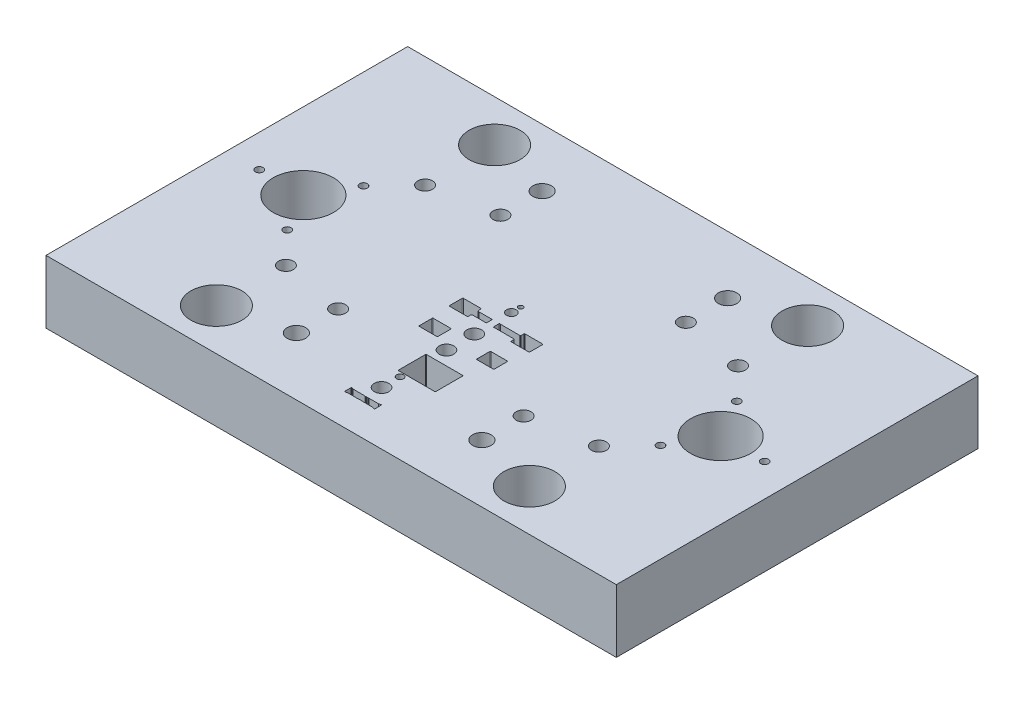
SolidWorks part; units mm, degrees
ref_plane "Front" through (0, 0, 0) normal (0, 0, 1) x (1, 0, 0)
ref_plane "Top" through (0, 0, 0) normal (0, 1, 0) x (1, 0, 0)
ref_plane "Right" through (0, 0, 0) normal (1, 0, 0) x (0, 0, -1)
sketch "Sketch1" plane through (0, 0, 0) normal (0, 0, 1) x (1, 0, 0)
  line L1 (-123, 0) -> (123, 0)
  line L2 (-123, 0) -> (-123, 27.2)
  line L3 (-123, 27.2) -> (123, 27.2)
  line L4 (123, 0) -> (123, 27.2)
  dimension "D1" = 246
  dimension "D2" = 27.2
extrude "Extrude1" add sketch "Sketch1" along normal mid plane 156
hole_wizard "Hole4" positions "Sketch9" profile "Sketch8" legacy
sketch "Sketch9" plane through (0, 0, 0) normal (0, -1, 0) x (1, 0, 0)
  line L0 (0, 0) -> (0, 38.3553) construction
  point P0 (90, 0)
  dimension "D1" = 180
sketch "Sketch8" plane through (90, 0, 0) normal (1, 0, 0) x (0, 0, -1)
  line L0 (0, 0) -> (0, 30)
  line L1 (0, 30) -> (13, 30)
  line L2 (13, 30) -> (13, 0)
  line L3 (13, 0) -> (0, 0)
  line L4 (0, 110) -> (0, -10) construction
  dimension "Diameter" = 26
  dimension "Depth" = 30
pattern_linear "LPattern4" count 2 spacing 180 along (-1, 0, 0) of "Hole4"
sketch "Sketch10" plane through (0, 0, 0) normal (0, 0, 1) x (1, 0, 0)
  line L1 (52.5, 27.2) -> (-52.5, 27.2)
  line L2 (52.5, 27.2) -> (52.5, 17.2)
  line L3 (52.5, 17.2) -> (-52.5, 17.2)
  line L4 (-52.5, 27.2) -> (-52.5, 17.2)
  line L5 (0, 17.2) -> (0, 0) construction
  line L6 (123, 27.2) -> (-123, 27.2) construction
  dimension "D1" = 10
  dimension "D2" = 105
extrude "Cut-Extrude1" [suppressed] cut sketch "Sketch10" against normal mid plane 206
hole_wizard "Hole5" positions "Sketch13" profile "Sketch12" legacy
sketch "Sketch13" plane through (0, 0, 0) normal (0, -1, 0) x (1, 0, 0)
  point P0 (-67.5, -30)
  dimension "D1" = 30
  dimension "D2" = 67.5
sketch "Sketch12" plane through (-67.5, 0, -30) normal (1, 0, 0) x (0, 0, -1)
  line L0 (0, 0) -> (0, 100)
  line L1 (0, 100) -> (3.2, 100)
  line L2 (3.2, 100) -> (3.2, 12)
  line L3 (3.2, 12) -> (12.5, 12)
  line L4 (12.5, 12) -> (12.5, 0)
  line L5 (12.5, 0) -> (0, 0)
  line L6 (0, 110) -> (0, -10) construction
  dimension "Diameter" = 6.4
  dimension "Depth" = 100
  dimension "C-Bore Diameter" = 25
  dimension "C-Bore Depth" = 12
cosmetic thread "Cosmetic Thread1" parameters "D2"=8
sketch "Sketch17" plane through (0, 0, 0) normal (0, -1, 0) x (1, 0, 0)
  line L0 (-20, 0) -> (20, 0) construction
  line L2 (-20, 70) -> (-20, -70)
  line L3 (-15, -75) -> (15, -75)
  line L4 (20, 70) -> (20, -70)
  line L6 (-15, 75) -> (15, 75)
  arc A0 (20, -70) -> (15, -75) centre (15, -70) cw
  arc A1 (-15, -75) -> (-20, -70) centre (-15, -70) cw
  arc A2 (15, 75) -> (20, 70) centre (15, 70) cw
  arc A5 (-15, 75) -> (-20, 70) centre (-15, 70) ccw
  point P8 (20, -75)
  point P13 (-50, 90)
  point P16 (50, 90)
  dimension "D4" = 5
  dimension "D1" = 75
  dimension "D2" = 75
  dimension "D3" = 40
extrude "Cut-Extrude4" cut sketch "Sketch17" against normal blind 1
pattern_linear "LPattern5" count 2 spacing 60 along (0, 0, 1) count 2 spacing 135 along (1, 0, 0) of "Hole5"
hole_wizard "CBORE for M6 Hex Socket Head Cap Screw1" positions "Sketch19" profile "Sketch18" counterbore size "M6" standard "ISO" end condition through all
sketch "Sketch19" plane through (0, 0, 0) normal (0, -1, 0) x (1, 0, 0)
  point P1 (40, 35)
  point P4 (40, -35)
  point P13 (-40, -35)
  point P16 (-40, 35)
sketch "Sketch18" plane through (40, 0, 35) normal (1, 0, 0) x (0, 0, -1)
  line L0 (0, 0) -> (0, 27.2)
  line L1 (0, 27.2) -> (3.2, 27.2)
  line L3 (3.2, 27.2) -> (3.2, 8)
  line L4 (3.2, 8) -> (5.5, 8)
  line L5 (5.5, 8) -> (5.5, 0)
  line L7 (5.5, 0) -> (0, 0)
  line L11 (0, -6.35) -> (0, 107.95) construction
  dimension "Thru Hole Dia." = 6.4
  dimension "Thru Hole Depth" = 27.2
  dimension "C'Bore Dia." = 11
  dimension "C'Bore Depth" = 8
hole_wizard "Hole6" positions "Sketch21" profile "Sketch20" legacy end condition through all
sketch "Sketch21" plane through (0, 0, 0) normal (0, -1, 0) x (1, 0, 0)
  point P1 (40, 53)
  point P8 (-40, 53)
  point P11 (-40, -53)
  point P14 (40, -53)
sketch "Sketch20" plane through (40, 0, 53) normal (1, 0, 0) x (0, 0, -1)
  line L0 (0, 0) -> (0, 27.2)
  line L1 (0, 27.2) -> (4, 27.2)
  line L2 (4, 27.2) -> (4, 0)
  line L3 (4, 0) -> (0, 0)
  line L4 (0, 110) -> (0, -10) construction
  dimension "Diameter" = 8
  dimension "Depth" = 27.2
hole_wizard "M4 Tapped Hole1" positions "Sketch23" profile "Sketch22" tap size "M4" standard "ISO" end condition through all
sketch "Sketch23" plane through (0, 0, 0) normal (0, -1, 0) x (1, 0, 0)
  line L2 (0, 0) -> (0, 17.7628) construction
  point P18 (-80.5, 16.4545)
  point P21 (-80.5, -16.4545)
  point P24 (-109, 0)
  point P27 (109, 0)
  point P30 (80.5, 16.4545)
  point P33 (80.5, -16.4545)
cosmetic thread "Hole Thread1" parameters "D2"=4
cosmetic thread "Hole Thread4" parameters "D2"=4
sketch "Sketch22" plane through (-80.5, 0, 16.4545) normal (1, 0, 0) x (0, 0, -1)
  line L0 (0, 0) -> (0, 27.2)
  line L1 (0, 27.2) -> (1.65, 27.2)
  line L2 (1.65, 27.2) -> (1.65, 0)
  line L5 (1.65, 0) -> (0, 0)
  line L11 (0, -6.35) -> (0, 107.95) construction
  dimension "Thru Tap Drill Dia." = 3.3
  dimension "Thru Tap Drill Depth" = 27.2
cosmetic thread "Hole Thread5" parameters "D2"=4
cosmetic thread "Hole Thread6" parameters "D2"=4
cosmetic thread "Hole Thread7" parameters "D2"=4
cosmetic thread "Hole Thread8" parameters "D2"=4
hole_wizard "Hole7" positions "Sketch25" profile "Sketch24" legacy end condition through all
sketch "Sketch25" plane through (0, 0, 0) normal (0, -1, 0) x (1, 0, 0)
  line L0 (0, 0) -> (0, 42.8622) construction
  line L1 (0, 0) -> (37.657, 0) construction
  point P0 (-67.5, 60)
  point P9 (67.5, 60)
  point P10 (67.5, -60)
  point P11 (-67.5, -60)
  dimension "D1" = 135
  dimension "D2" = 120
sketch "Sketch24" plane through (-67.5, 0, 60) normal (1, 0, 0) x (0, 0, -1)
  line L0 (0, 0) -> (0, 27.2)
  line L1 (0, 27.2) -> (11, 27.2)
  line L2 (11, 27.2) -> (11, 0)
  line L3 (11, 0) -> (0, 0)
  line L4 (0, 110) -> (0, -10) construction
  dimension "Diameter" = 22
  dimension "Depth" = 27.2
sketch "Sketch27" plane through (0, 0, 0) normal (0, -1, 0) x (1, 0, 0)
  line L0 (17.43, 4.3) -> (17.43, 9.7)
  line L1 (17.15, 9.98) -> (9.65, 9.98)
  line L2 (9.37, 9.7) -> (9.37, 8.5894)
  line L3 (9.269, 8.4043) -> (9.1455, 8.325)
  line L4 (8.635, 23.75) -> (8.635, 18.25)
  line L5 (8.9, 17.985) -> (15.9, 17.985)
  line L6 (-6.7858, 64.265) -> (-7.4288, 64.499) construction
  line L7 (-7.7844, 64.25) -> (-7.7844, 61.75) construction
  line L8 (-7.4288, 61.501) -> (-6.7858, 61.735) construction
  line L9 (4.89, 64.499) -> (4.247, 64.265) construction
  line L10 (5.2456, 61.75) -> (5.2456, 64.25) construction
  line L11 (4.247, 61.735) -> (4.89, 61.501) construction
  line L12 (4.247, 64.265) -> (0.0046, 64.265) construction
  line L13 (-1.7954, 64.265) -> (-6.7858, 64.265) construction
  line L14 (0.0046, 61.735) -> (4.247, 61.735) construction
  line L15 (-6.7858, 61.735) -> (-1.7954, 61.735) construction
  line L16 (-6.7858, 64.265) -> (-7.4288, 64.499) construction
  line L17 (-7.7844, 64.25) -> (-7.7844, 61.75) construction
  line L18 (16.165, 18.25) -> (16.165, 23.75)
  line L19 (15.9, 24.015) -> (8.9, 24.015)
  line L20 (8.635, 23.75) -> (8.635, 18.25) construction
  line L21 (8.9, 17.985) -> (15.9, 17.985) construction
  line L22 (16.165, 18.25) -> (16.165, 23.75) construction
  line L23 (15.9, 24.015) -> (8.9, 24.015) construction
  line L24 (17.415, 4.3) -> (17.415, 9.7)
  line L25 (9.65, 4.035) -> (17.15, 4.035)
  line L26 (9.385, 5.4106) -> (9.385, 4.3)
  line L27 (9.1537, 5.6877) -> (9.2771, 5.6083)
  line L28 (0.7046, 5.725) -> (9.0266, 5.725)
  line L29 (0.5972, 5.701) -> (0.6243, 5.7108)
  line L30 (0.2416, 8.05) -> (0.2416, 5.95)
  line L31 (0.6243, 8.2892) -> (0.5972, 8.299)
  line L32 (9.0266, 8.275) -> (0.7046, 8.275)
  line L33 (9.2771, 8.3917) -> (9.1537, 8.3123)
  line L34 (9.385, 9.7) -> (9.385, 8.5894)
  line L35 (17.15, 9.965) -> (9.65, 9.965)
  line L36 (17.415, 4.3) -> (17.415, 9.7) construction
  line L37 (9.65, 4.035) -> (17.15, 4.035) construction
  line L38 (9.385, 5.4106) -> (9.385, 4.3) construction
  line L39 (9.1537, 5.6877) -> (9.2771, 5.6083) construction
  line L40 (0.7046, 5.725) -> (9.0266, 5.725) construction
  line L41 (0.5972, 5.701) -> (0.6243, 5.7108) construction
  line L42 (0.2416, 8.05) -> (0.2416, 5.95) construction
  line L43 (0.6243, 8.2892) -> (0.5972, 8.299) construction
  line L44 (9.0266, 8.275) -> (0.7046, 8.275) construction
  line L45 (9.2771, 8.3917) -> (9.1537, 8.3123) construction
  line L46 (9.385, 9.7) -> (9.385, 8.5894) construction
  line L47 (17.15, 9.965) -> (9.65, 9.965) construction
  line L48 (-3.136, 8.309) -> (-3.1905, 8.2892)
  line L49 (-3.2709, 8.275) -> (-8.5069, 8.275)
  line L50 (-8.5775, 8.2858) -> (-8.9624, 8.407)
  line L51 (-9.1604, 9) -> (-9.1604, 9.7)
  line L52 (-9.4254, 9.965) -> (-16.9254, 9.965)
  line L53 (-17.1904, 9.7) -> (-17.1904, 4.3)
  line L54 (-16.9254, 4.035) -> (-9.4254, 4.035)
  line L55 (-9.1604, 4.3) -> (-9.1604, 5)
  line L56 (-8.9624, 5.593) -> (-8.5775, 5.7142)
  line L57 (-8.5069, 5.725) -> (-3.2709, 5.725)
  line L58 (-3.1905, 5.7108) -> (-3.136, 5.691)
  line L59 (-2.7804, 5.94) -> (-2.7804, 8.06)
  line L60 (-3.136, 8.309) -> (-3.1905, 8.2892) construction
  line L61 (-3.2709, 8.275) -> (-8.5069, 8.275) construction
  line L62 (-8.5775, 8.2858) -> (-8.9624, 8.407) construction
  line L63 (-9.1604, 9) -> (-9.1604, 9.7) construction
  line L64 (-9.4254, 9.965) -> (-16.9254, 9.965) construction
  line L65 (-17.1904, 9.7) -> (-17.1904, 4.3) construction
  line L66 (-16.9254, 4.035) -> (-9.4254, 4.035) construction
  line L67 (-9.1604, 4.3) -> (-9.1604, 5) construction
  line L68 (-8.9624, 5.593) -> (-8.5775, 5.7142) construction
  line L69 (-8.5069, 5.725) -> (-3.2709, 5.725) construction
  line L70 (-3.1905, 5.7108) -> (-3.136, 5.691) construction
  line L71 (-2.7804, 5.94) -> (-2.7804, 8.06) construction
  line L72 (11.9196, 33.25) -> (11.9196, 44.75)
  line L73 (11.6546, 45.015) -> (-3.8454, 45.015)
  line L74 (-4.1104, 44.75) -> (-4.1104, 33.25)
  line L75 (-3.8454, 32.985) -> (11.6546, 32.985)
  line L76 (11.9196, 33.25) -> (11.9196, 44.75) construction
  line L77 (11.6546, 45.015) -> (-3.8454, 45.015) construction
  line L78 (-4.1104, 44.75) -> (-4.1104, 33.25) construction
  line L79 (-3.8454, 32.985) -> (11.6546, 32.985) construction
  line L80 (-16.2104, 23.75) -> (-16.2104, 18.25)
  line L81 (-15.9454, 17.985) -> (-8.4454, 17.985)
  line L82 (-8.1804, 18.25) -> (-8.1804, 23.75)
  line L83 (-8.4454, 24.015) -> (-15.9454, 24.015)
  line L84 (-16.2104, 23.75) -> (-16.2104, 18.25) construction
  line L85 (-15.9454, 17.985) -> (-8.4454, 17.985) construction
  line L86 (-8.1804, 18.25) -> (-8.1804, 23.75) construction
  line L87 (-8.4454, 24.015) -> (-15.9454, 24.015) construction
  line L88 (9.0266, 8.29) -> (0.7046, 8.29)
  line L89 (0.6294, 8.3033) -> (0.6023, 8.3131)
  line L90 (0.2266, 8.05) -> (0.2266, 5.95)
  line L91 (0.6023, 5.6869) -> (0.6294, 5.6967)
  line L92 (0.7046, 5.71) -> (9.0266, 5.71)
  line L93 (9.1455, 5.675) -> (9.269, 5.5957)
  line L94 (9.37, 5.4106) -> (9.37, 4.3)
  line L95 (9.65, 4.02) -> (17.15, 4.02)
  line L96 (-3.1411, 8.3231) -> (-3.1957, 8.3033)
  line L97 (-3.2709, 8.29) -> (-8.5069, 8.29)
  line L98 (-8.573, 8.3002) -> (-8.9579, 8.4213)
  line L99 (-9.1454, 9) -> (-9.1454, 9.7)
  line L100 (-9.4254, 9.98) -> (-16.9254, 9.98)
  line L101 (-17.2054, 9.7) -> (-17.2054, 4.3)
  line L102 (-16.9254, 4.02) -> (-9.4254, 4.02)
  line L103 (-9.1454, 4.3) -> (-9.1454, 5)
  line L104 (-8.9579, 5.5787) -> (-8.573, 5.6998)
  line L105 (-8.5069, 5.71) -> (-3.2709, 5.71)
  line L106 (-3.1957, 5.6967) -> (-3.1411, 5.6769)
  line L107 (-2.7654, 5.94) -> (-2.7654, 8.06)
  line L108 (-16.2254, 23.75) -> (-16.2254, 18.25)
  line L109 (-15.9454, 17.97) -> (-8.4454, 17.97)
  line L110 (-8.1654, 18.25) -> (-8.1654, 23.75)
  line L111 (-8.4454, 24.03) -> (-15.9454, 24.03)
  line L112 (8.62, 23.75) -> (8.62, 18.25)
  line L113 (8.9, 17.97) -> (15.9, 17.97)
  line L114 (16.18, 18.25) -> (16.18, 23.75)
  line L115 (15.9, 24.03) -> (8.9, 24.03)
  line L116 (11.9346, 33.25) -> (11.9346, 44.75)
  line L117 (11.6546, 45.03) -> (-3.8454, 45.03)
  line L118 (-4.1254, 44.75) -> (-4.1254, 33.25)
  line L119 (-3.8454, 32.97) -> (11.6546, 32.97)
  line L120 (-7.4288, 61.501) -> (-6.7858, 61.735) construction
  line L121 (4.89, 64.499) -> (4.247, 64.265) construction
  line L122 (5.2456, 61.75) -> (5.2456, 64.25) construction
  line L123 (4.247, 61.735) -> (4.89, 61.501) construction
  line L124 (4.247, 64.265) -> (0.0046, 64.265) construction
  line L125 (-1.7954, 64.265) -> (-6.7858, 64.265) construction
  line L126 (0.0046, 61.735) -> (4.247, 61.735) construction
  line L127 (-6.7858, 61.735) -> (-1.7954, 61.735) construction
  line L128 (-6.7831, 64.28) -> (-7.4236, 64.5131)
  line L129 (-7.7994, 64.25) -> (-7.7994, 61.75)
  line L130 (-7.4236, 61.4869) -> (-6.7831, 61.72)
  line L131 (-6.7831, 61.72) -> (-1.7954, 61.72)
  line L132 (0.0046, 61.72) -> (4.2444, 61.72)
  line L133 (4.2444, 61.72) -> (4.8848, 61.4869)
  line L212 (5.2606, 61.75) -> (5.2606, 64.25)
  line L213 (4.8848, 64.5131) -> (4.2444, 64.28)
  line L214 (4.2444, 64.28) -> (0.0046, 64.28)
  line L215 (-1.7954, 64.28) -> (-6.7831, 64.28)
  arc A0 (17.43, 9.7) -> (17.15, 9.98) centre (17.15, 9.7) ccw
  arc A1 (9.65, 9.98) -> (9.37, 9.7) centre (9.65, 9.7) ccw
  arc A2 (9.269, 8.4043) -> (9.37, 8.5894) centre (9.15, 8.5894) ccw
  arc A3 (9.0266, 8.29) -> (9.1455, 8.325) centre (9.0266, 8.51) ccw
  arc A4 (8.635, 18.25) -> (8.9, 17.985) centre (8.9, 18.25) ccw
  arc A5 (15.9, 17.985) -> (16.165, 18.25) centre (15.9, 18.25) ccw
  arc A6 (16.165, 23.75) -> (15.9, 24.015) centre (15.9, 23.75) ccw
  arc A7 (8.9, 24.015) -> (8.635, 23.75) centre (8.9, 23.75) ccw
  arc A8 (8.635, 18.25) -> (8.9, 17.985) centre (8.9, 18.25) ccw construction
  arc A9 (15.9, 17.985) -> (16.165, 18.25) centre (15.9, 18.25) ccw construction
  arc A10 (16.165, 23.75) -> (15.9, 24.015) centre (15.9, 23.75) ccw construction
  arc A11 (8.9, 24.015) -> (8.635, 23.75) centre (8.9, 23.75) ccw construction
  arc A12 (17.15, 4.035) -> (17.415, 4.3) centre (17.15, 4.3) ccw
  arc A13 (9.385, 4.3) -> (9.65, 4.035) centre (9.65, 4.3) ccw
  arc A14 (9.385, 5.4106) -> (9.2771, 5.6083) centre (9.15, 5.4106) ccw
  arc A15 (9.1537, 5.6877) -> (9.0266, 5.725) centre (9.0266, 5.49) ccw
  arc A16 (0.7046, 5.725) -> (0.6243, 5.7108) centre (0.7046, 5.49) ccw
  arc A17 (0.2416, 5.95) -> (0.5972, 5.701) centre (0.5066, 5.95) ccw
  arc A18 (-7.4288, 64.499) -> (-7.7844, 64.25) centre (-7.5194, 64.25) ccw construction
  arc A19 (-7.7844, 61.75) -> (-7.4288, 61.501) centre (-7.5194, 61.75) ccw construction
  arc A20 (5.2456, 64.25) -> (4.89, 64.499) centre (4.9806, 64.25) ccw construction
  arc A21 (4.89, 61.501) -> (5.2456, 61.75) centre (4.9806, 61.75) ccw construction
  arc A22 (0.0046, 64.265) -> (-0.1544, 64.212) centre (0.0046, 64) ccw construction
  arc A23 (-0.4364, 64.212) -> (-0.1544, 64.212) centre (-0.2954, 64.4) ccw construction
  arc A24 (-0.4364, 64.212) -> (-0.7544, 64.212) centre (-0.5954, 64) ccw construction
  arc A25 (-1.0364, 64.212) -> (-0.7544, 64.212) centre (-0.8954, 64.4) ccw construction
  arc A26 (-1.0364, 64.212) -> (-1.3544, 64.212) centre (-1.1954, 64) ccw construction
  arc A27 (-1.6364, 64.212) -> (-1.3544, 64.212) centre (-1.4954, 64.4) ccw construction
  arc A28 (-1.6364, 64.212) -> (-1.7954, 64.265) centre (-1.7954, 64) ccw construction
  arc A29 (-0.1544, 61.788) -> (0.0046, 61.735) centre (0.0046, 62) ccw construction
  arc A30 (-0.1544, 61.788) -> (-0.4364, 61.788) centre (-0.2954, 61.6) ccw construction
  arc A31 (-0.7544, 61.788) -> (-0.4364, 61.788) centre (-0.5954, 62) ccw construction
  arc A32 (-0.7544, 61.788) -> (-1.0364, 61.788) centre (-0.8954, 61.6) ccw construction
  arc A33 (-1.3544, 61.788) -> (-1.0364, 61.788) centre (-1.1954, 62) ccw construction
  arc A34 (-1.3544, 61.788) -> (-1.6364, 61.788) centre (-1.4954, 61.6) ccw construction
  arc A35 (-1.7954, 61.735) -> (-1.6364, 61.788) centre (-1.7954, 62) ccw construction
  arc A36 (-7.4288, 64.499) -> (-7.7844, 64.25) centre (-7.5194, 64.25) ccw construction
  arc A37 (-7.7844, 61.75) -> (-7.4288, 61.501) centre (-7.5194, 61.75) ccw construction
  arc A38 (5.2456, 64.25) -> (4.89, 64.499) centre (4.9806, 64.25) ccw construction
  arc A39 (4.89, 61.501) -> (5.2456, 61.75) centre (4.9806, 61.75) ccw construction
  arc A40 (0.0046, 64.265) -> (-0.1544, 64.212) centre (0.0046, 64) ccw construction
  arc A41 (-0.4364, 64.212) -> (-0.1544, 64.212) centre (-0.2954, 64.4) ccw construction
  arc A42 (-0.4364, 64.212) -> (-0.7544, 64.212) centre (-0.5954, 64) ccw construction
  arc A43 (-1.0364, 64.212) -> (-0.7544, 64.212) centre (-0.8954, 64.4) ccw construction
  arc A44 (-1.0364, 64.212) -> (-1.3544, 64.212) centre (-1.1954, 64) ccw construction
  arc A45 (-1.6364, 64.212) -> (-1.3544, 64.212) centre (-1.4954, 64.4) ccw construction
  arc A46 (-1.6364, 64.212) -> (-1.7954, 64.265) centre (-1.7954, 64) ccw construction
  arc A47 (-0.1544, 61.788) -> (0.0046, 61.735) centre (0.0046, 62) ccw construction
  arc A48 (-0.1544, 61.788) -> (-0.4364, 61.788) centre (-0.2954, 61.6) ccw construction
  arc A49 (-0.7544, 61.788) -> (-0.4364, 61.788) centre (-0.5954, 62) ccw construction
  arc A50 (-0.7544, 61.788) -> (-1.0364, 61.788) centre (-0.8954, 61.6) ccw construction
  arc A51 (-1.3544, 61.788) -> (-1.0364, 61.788) centre (-1.1954, 62) ccw construction
  arc A52 (-1.3544, 61.788) -> (-1.6364, 61.788) centre (-1.4954, 61.6) ccw construction
  arc A53 (-1.7954, 61.735) -> (-1.6364, 61.788) centre (-1.7954, 62) ccw construction
  arc A54 (0.5972, 8.299) -> (0.2416, 8.05) centre (0.5066, 8.05) ccw
  arc A55 (0.6243, 8.2892) -> (0.7046, 8.275) centre (0.7046, 8.51) ccw
  arc A56 (9.0266, 8.275) -> (9.1537, 8.3123) centre (9.0266, 8.51) ccw
  arc A57 (9.2771, 8.3917) -> (9.385, 8.5894) centre (9.15, 8.5894) ccw
  arc A58 (9.65, 9.965) -> (9.385, 9.7) centre (9.65, 9.7) ccw
  arc A59 (17.415, 9.7) -> (17.15, 9.965) centre (17.15, 9.7) ccw
  arc A60 (17.15, 4.035) -> (17.415, 4.3) centre (17.15, 4.3) ccw construction
  arc A61 (9.385, 4.3) -> (9.65, 4.035) centre (9.65, 4.3) ccw construction
  arc A62 (9.385, 5.4106) -> (9.2771, 5.6083) centre (9.15, 5.4106) ccw construction
  arc A63 (9.1537, 5.6877) -> (9.0266, 5.725) centre (9.0266, 5.49) ccw construction
  arc A64 (0.7046, 5.725) -> (0.6243, 5.7108) centre (0.7046, 5.49) ccw construction
  arc A65 (0.2416, 5.95) -> (0.5972, 5.701) centre (0.5066, 5.95) ccw construction
  arc A66 (0.5972, 8.299) -> (0.2416, 8.05) centre (0.5066, 8.05) ccw construction
  arc A67 (0.6243, 8.2892) -> (0.7046, 8.275) centre (0.7046, 8.51) ccw construction
  arc A68 (9.0266, 8.275) -> (9.1537, 8.3123) centre (9.0266, 8.51) ccw construction
  arc A69 (9.2771, 8.3917) -> (9.385, 8.5894) centre (9.15, 8.5894) ccw construction
  arc A70 (9.65, 9.965) -> (9.385, 9.7) centre (9.65, 9.7) ccw construction
  arc A71 (17.415, 9.7) -> (17.15, 9.965) centre (17.15, 9.7) ccw construction
  arc A72 (11.9196, 44.75) -> (11.6546, 45.015) centre (11.6546, 44.75) ccw
  arc A73 (-3.8454, 45.015) -> (-4.1104, 44.75) centre (-3.8454, 44.75) ccw
  arc A74 (-4.1104, 33.25) -> (-3.8454, 32.985) centre (-3.8454, 33.25) ccw
  arc A75 (11.6546, 32.985) -> (11.9196, 33.25) centre (11.6546, 33.25) ccw
  arc A76 (-3.2709, 8.275) -> (-3.1905, 8.2892) centre (-3.2709, 8.51) ccw
  arc A77 (-8.5775, 8.2858) -> (-8.5069, 8.275) centre (-8.5069, 8.51) ccw
  arc A78 (-9.0584, 8.4774) -> (-8.9624, 8.407) centre (-8.9068, 8.5835) ccw
  arc A79 (-9.0821, 8.5242) -> (-9.0584, 8.4774) centre (-8.9068, 8.5835) ccw
  arc A80 (-9.1604, 9) -> (-9.0821, 8.5242) centre (-7.6754, 9) ccw
  arc A81 (-9.1604, 9.7) -> (-9.4254, 9.965) centre (-9.4254, 9.7) ccw
  arc A82 (-16.9254, 9.965) -> (-17.1904, 9.7) centre (-16.9254, 9.7) ccw
  arc A83 (-17.1904, 4.3) -> (-16.9254, 4.035) centre (-16.9254, 4.3) ccw
  arc A84 (-9.4254, 4.035) -> (-9.1604, 4.3) centre (-9.4254, 4.3) ccw
  arc A85 (-9.0821, 5.4758) -> (-9.1604, 5) centre (-7.6754, 5) ccw
  arc A86 (-9.0584, 5.5226) -> (-9.0821, 5.4758) centre (-8.9068, 5.4165) ccw
  arc A87 (-8.9624, 5.593) -> (-9.0584, 5.5226) centre (-8.9068, 5.4165) ccw
  arc A88 (-8.5069, 5.725) -> (-8.5775, 5.7142) centre (-8.5069, 5.49) ccw
  arc A89 (-3.1905, 5.7108) -> (-3.2709, 5.725) centre (-3.2709, 5.49) ccw
  arc A90 (-3.136, 5.691) -> (-2.7804, 5.94) centre (-3.0454, 5.94) ccw
  arc A91 (-2.7804, 8.06) -> (-3.136, 8.309) centre (-3.0454, 8.06) ccw
  arc A92 (-3.2709, 8.275) -> (-3.1905, 8.2892) centre (-3.2709, 8.51) ccw construction
  arc A93 (-8.5775, 8.2858) -> (-8.5069, 8.275) centre (-8.5069, 8.51) ccw construction
  arc A94 (-9.0584, 8.4774) -> (-8.9624, 8.407) centre (-8.9068, 8.5835) ccw construction
  arc A95 (-9.0821, 8.5242) -> (-9.0584, 8.4774) centre (-8.9068, 8.5835) ccw construction
  arc A96 (-9.1604, 9) -> (-9.0821, 8.5242) centre (-7.6754, 9) ccw construction
  arc A97 (-9.1604, 9.7) -> (-9.4254, 9.965) centre (-9.4254, 9.7) ccw construction
  arc A98 (-16.9254, 9.965) -> (-17.1904, 9.7) centre (-16.9254, 9.7) ccw construction
  arc A99 (-17.1904, 4.3) -> (-16.9254, 4.035) centre (-16.9254, 4.3) ccw construction
  arc A100 (-9.4254, 4.035) -> (-9.1604, 4.3) centre (-9.4254, 4.3) ccw construction
  arc A101 (-9.0821, 5.4758) -> (-9.1604, 5) centre (-7.6754, 5) ccw construction
  arc A102 (-9.0584, 5.5226) -> (-9.0821, 5.4758) centre (-8.9068, 5.4165) ccw construction
  arc A103 (-8.9624, 5.593) -> (-9.0584, 5.5226) centre (-8.9068, 5.4165) ccw construction
  arc A104 (-8.5069, 5.725) -> (-8.5775, 5.7142) centre (-8.5069, 5.49) ccw construction
  arc A105 (-3.1905, 5.7108) -> (-3.2709, 5.725) centre (-3.2709, 5.49) ccw construction
  arc A106 (-3.136, 5.691) -> (-2.7804, 5.94) centre (-3.0454, 5.94) ccw construction
  arc A107 (-2.7804, 8.06) -> (-3.136, 8.309) centre (-3.0454, 8.06) ccw construction
  arc A108 (11.9196, 44.75) -> (11.6546, 45.015) centre (11.6546, 44.75) ccw construction
  arc A109 (-3.8454, 45.015) -> (-4.1104, 44.75) centre (-3.8454, 44.75) ccw construction
  arc A110 (-4.1104, 33.25) -> (-3.8454, 32.985) centre (-3.8454, 33.25) ccw construction
  arc A111 (11.6546, 32.985) -> (11.9196, 33.25) centre (11.6546, 33.25) ccw construction
  arc A112 (-16.2104, 18.25) -> (-15.9454, 17.985) centre (-15.9454, 18.25) ccw
  arc A113 (-8.4454, 17.985) -> (-8.1804, 18.25) centre (-8.4454, 18.25) ccw
  arc A114 (-8.1804, 23.75) -> (-8.4454, 24.015) centre (-8.4454, 23.75) ccw
  arc A115 (-15.9454, 24.015) -> (-16.2104, 23.75) centre (-15.9454, 23.75) ccw
  arc A116 (-16.2104, 18.25) -> (-15.9454, 17.985) centre (-15.9454, 18.25) ccw construction
  arc A117 (-8.4454, 17.985) -> (-8.1804, 18.25) centre (-8.4454, 18.25) ccw construction
  arc A118 (-8.1804, 23.75) -> (-8.4454, 24.015) centre (-8.4454, 23.75) ccw construction
  arc A119 (-15.9454, 24.015) -> (-16.2104, 23.75) centre (-15.9454, 23.75) ccw construction
  arc A120 (0.6294, 8.3033) -> (0.7046, 8.29) centre (0.7046, 8.51) ccw
  arc A121 (0.6023, 8.3131) -> (0.2266, 8.05) centre (0.5066, 8.05) ccw
  arc A122 (0.2266, 5.95) -> (0.6023, 5.6869) centre (0.5066, 5.95) ccw
  arc A123 (0.7046, 5.71) -> (0.6294, 5.6967) centre (0.7046, 5.49) ccw
  arc A124 (9.1455, 5.675) -> (9.0266, 5.71) centre (9.0266, 5.49) ccw
  arc A125 (9.37, 5.4106) -> (9.269, 5.5957) centre (9.15, 5.4106) ccw
  arc A126 (9.37, 4.3) -> (9.65, 4.02) centre (9.65, 4.3) ccw
  arc A127 (17.15, 4.02) -> (17.43, 4.3) centre (17.15, 4.3) ccw
  arc A128 (-3.2709, 8.29) -> (-3.1957, 8.3033) centre (-3.2709, 8.51) ccw
  arc A129 (-8.573, 8.3002) -> (-8.5069, 8.29) centre (-8.5069, 8.51) ccw
  arc A130 (-9.0461, 8.486) -> (-8.9579, 8.4213) centre (-8.9068, 8.5835) ccw
  arc A131 (-9.0679, 8.529) -> (-9.0461, 8.486) centre (-8.9068, 8.5835) ccw
  arc A132 (-9.1454, 9) -> (-9.0679, 8.529) centre (-7.6754, 9) ccw
  arc A133 (-9.1454, 9.7) -> (-9.4254, 9.98) centre (-9.4254, 9.7) ccw
  arc A134 (-16.9254, 9.98) -> (-17.2054, 9.7) centre (-16.9254, 9.7) ccw
  arc A135 (-17.2054, 4.3) -> (-16.9254, 4.02) centre (-16.9254, 4.3) ccw
  arc A136 (-9.4254, 4.02) -> (-9.1454, 4.3) centre (-9.4254, 4.3) ccw
  arc A137 (-9.0679, 5.471) -> (-9.1454, 5) centre (-7.6754, 5) ccw
  arc A138 (-9.0461, 5.514) -> (-9.0679, 5.471) centre (-8.9068, 5.4165) ccw
  arc A139 (-8.9579, 5.5787) -> (-9.0461, 5.514) centre (-8.9068, 5.4165) ccw
  arc A140 (-8.5069, 5.71) -> (-8.573, 5.6998) centre (-8.5069, 5.49) ccw
  arc A141 (-3.1957, 5.6967) -> (-3.2709, 5.71) centre (-3.2709, 5.49) ccw
  arc A142 (-3.1411, 5.6769) -> (-2.7654, 5.94) centre (-3.0454, 5.94) ccw
  arc A143 (-2.7654, 8.06) -> (-3.1411, 8.3231) centre (-3.0454, 8.06) ccw
  arc A144 (-16.2254, 18.25) -> (-15.9454, 17.97) centre (-15.9454, 18.25) ccw
  arc A145 (-8.4454, 17.97) -> (-8.1654, 18.25) centre (-8.4454, 18.25) ccw
  arc A146 (-8.1654, 23.75) -> (-8.4454, 24.03) centre (-8.4454, 23.75) ccw
  arc A147 (-15.9454, 24.03) -> (-16.2254, 23.75) centre (-15.9454, 23.75) ccw
  arc A148 (8.62, 18.25) -> (8.9, 17.97) centre (8.9, 18.25) ccw
  arc A149 (15.9, 17.97) -> (16.18, 18.25) centre (15.9, 18.25) ccw
  arc A150 (16.18, 23.75) -> (15.9, 24.03) centre (15.9, 23.75) ccw
  arc A151 (8.9, 24.03) -> (8.62, 23.75) centre (8.9, 23.75) ccw
  arc A152 (11.9346, 44.75) -> (11.6546, 45.03) centre (11.6546, 44.75) ccw
  arc A153 (-3.8454, 45.03) -> (-4.1254, 44.75) centre (-3.8454, 44.75) ccw
  arc A154 (-4.1254, 33.25) -> (-3.8454, 32.97) centre (-3.8454, 33.25) ccw
  arc A155 (11.6546, 32.97) -> (11.9346, 33.25) centre (11.6546, 33.25) ccw
  arc A158 (-7.4236, 64.5131) -> (-7.7994, 64.25) centre (-7.5194, 64.25) ccw
  arc A159 (-7.7994, 61.75) -> (-7.4236, 61.4869) centre (-7.5194, 61.75) ccw
  arc A160 (-1.7954, 61.72) -> (-1.6274, 61.776) centre (-1.7954, 62) ccw
  arc A161 (-1.3634, 61.776) -> (-1.6274, 61.776) centre (-1.4954, 61.6) ccw
  arc A162 (-1.3634, 61.776) -> (-1.0274, 61.776) centre (-1.1954, 62) ccw
  arc A163 (-0.7634, 61.776) -> (-1.0274, 61.776) centre (-0.8954, 61.6) ccw
  arc A164 (-0.7634, 61.776) -> (-0.4274, 61.776) centre (-0.5954, 62) ccw
  arc A167 (-0.1634, 61.776) -> (-0.4274, 61.776) centre (-0.2954, 61.6) ccw
  arc A168 (-0.1634, 61.776) -> (0.0046, 61.72) centre (0.0046, 62) ccw
  arc A169 (4.8848, 61.4869) -> (5.2606, 61.75) centre (4.9806, 61.75) ccw
  arc A170 (5.2606, 64.25) -> (4.8848, 64.5131) centre (4.9806, 64.25) ccw
  arc A171 (0.0046, 64.28) -> (-0.1634, 64.224) centre (0.0046, 64) ccw
  arc A172 (-0.4274, 64.224) -> (-0.1634, 64.224) centre (-0.2954, 64.4) ccw
  arc A173 (-0.4274, 64.224) -> (-0.7634, 64.224) centre (-0.5954, 64) ccw
  arc A174 (-1.0274, 64.224) -> (-0.7634, 64.224) centre (-0.8954, 64.4) ccw
  arc A175 (-1.0274, 64.224) -> (-1.3634, 64.224) centre (-1.1954, 64) ccw
  arc A176 (-1.6274, 64.224) -> (-1.3634, 64.224) centre (-1.4954, 64.4) ccw
  arc A177 (-1.6274, 64.224) -> (-1.7954, 64.28) centre (-1.7954, 64) ccw
  dimension "D2" = 0
  dimension "D3" = 0
  dimension "D4" = 0
  dimension "D5" = 0
  dimension "D6" = 0
  dimension "D7" = 0.015
  dimension "D8" = 0.015
  dimension "D9" = 0.015
  dimension "D10" = 0.015
  dimension "D11" = 0.015
  dimension "D12" = 0.015
extrude "Cut-Extrude5" cut sketch "Sketch27" against normal through all
hole_wizard "Hole8" positions "Sketch29" profile "Sketch28" legacy
sketch "Sketch29" plane through (0, 27.2, 0) normal (0, 1, 0) x (1, 0, 0)
  point P0 (-1.2694, 1)
sketch "Sketch28" plane through (-1.2694, 27.2, -1) normal (1, 0, 0) x (0, 0, 1)
  line L0 (0, 0) -> (0, 20)
  line L1 (0, 20) -> (2.1, 20)
  line L2 (2.1, 20) -> (2.1, 0)
  line L3 (2.1, 0) -> (0, 0)
  line L4 (0, 110) -> (0, -10) construction
  dimension "Diameter" = 4.2
  dimension "Depth" = 20
hole_wizard "Hole9" positions "Sketch31" profile "Sketch30" legacy
sketch "Sketch31" plane through (0, 27.2, 0) normal (0, 1, 0) x (1, 0, 0)
  point P0 (-1.2694, -15)
  point P3 (-1.2694, -27)
  point P6 (-1.2694, -55)
sketch "Sketch30" plane through (-1.2694, 27.2, 15) normal (1, 0, 0) x (0, 0, 1)
  line L0 (0, 0) -> (0, 20)
  line L1 (0, 20) -> (3.15, 20)
  line L2 (3.15, 20) -> (3.15, 0)
  line L3 (3.15, 0) -> (0, 0)
  line L4 (0, 110) -> (0, -10) construction
  dimension "Diameter" = 6.3
  dimension "Depth" = 20
hole_wizard "Hole10" positions "Sketch34" profile "Sketch33" legacy end condition through all
sketch "Sketch34" plane through (0, 0, 0) normal (0, -1, 0) x (-1, 0, 0)
  point P0 (1.2694, 5)
sketch "Sketch33" plane through (-1.2694, 0, -5) normal (1, 0, 0) x (0, 0, -1)
  line L0 (0, 0) -> (0, 27.2)
  line L1 (0, 27.2) -> (1.03, 27.2)
  line L2 (1.03, 27.2) -> (1.03, 0)
  line L3 (1.03, 0) -> (0, 0)
  line L4 (0, 110) -> (0, -10) construction
  dimension "Diameter" = 2.06
  dimension "Depth" = 27.2
hole_wizard "Hole11" positions "Sketch37" profile "Sketch36" legacy end condition through all
sketch "Sketch37" plane through (0, 27.2, 0) normal (0, 1, 0) x (1, 0, 0)
  point P0 (-1.2694, -47)
sketch "Sketch36" plane through (-1.2694, 27.2, 47) normal (1, 0, 0) x (0, 0, 1)
  line L0 (0, 0) -> (0, 27.2)
  line L1 (0, 27.2) -> (0.75, 27.2)
  line L2 (0.75, 27.2) -> (0.75, 18)
  line L3 (0.75, 18) -> (1.5, 18)
  line L4 (1.5, 18) -> (1.5, 0)
  line L5 (1.5, 0) -> (0, 0)
  line L6 (0, 110) -> (0, -10) construction
  dimension "Diameter" = 1.5
  dimension "Depth" = 27.2
  dimension "C-Bore Diameter" = 3
  dimension "C-Bore Depth" = 18
sketch "Sketch38" plane through (0, 0, 0) normal (0, -1, 0) x (1, 0, 0)
  line L0 (-26, 38) -> (-6, 38) construction
  line L1 (-5.5, 60.5) -> (-26.5, 60.5)
  line L2 (-5.5, 60.5) -> (-5.5, 37.5)
  line L3 (-5.5, 37.5) -> (-26.5, 37.5)
  line L4 (-26.5, 60.5) -> (-26.5, 37.5)
  line L5 (-26, 60) -> (-6, 60) construction
  line L6 (-6, 38) -> (-6, 60) construction
  line L7 (-26, 38) -> (-26, 60) construction
  dimension "D1" = 0.5
  dimension "D2" = 0.5
  dimension "D3" = 0.5
  dimension "D4" = 0.5
extrude "Cut-Extrude6" cut sketch "Sketch38" against normal up to vertex (6 mm away)
sketch "Sketch39" plane through (0, 0, 0) normal (0, -1, 0) x (1, 0, 0)
  line L0 (-5.5, 60.5) -> (-5.5, 37.5) construction
  line L1 (-5.5, 45.7818) -> (-0.5, 45.7818)
  line L2 (-5.5, 45.7818) -> (-5.5, 50.2818)
  line L3 (-5.5, 50.2818) -> (-0.5, 50.2818)
  line L4 (-26.5, 60.5) -> (-26.5, 37.5) construction
  line L5 (-6.7874, 50) -> (-6.7874, 46.0635) construction
  line L6 (-6, 50) -> (-26, 50) construction
  line L7 (-26, 46.0635) -> (-6, 46.0635) construction
  line L8 (-6.7874, 48.0318) -> (-5.5, 48.0318) construction
  line L9 (-26.5, 50.2818) -> (-33.5, 50.2818)
  line L10 (-26.5, 50.2818) -> (-26.5, 45.7818)
  line L11 (-26.5, 45.7818) -> (-33.5, 45.7818)
  arc A0 (-0.5, 50.2818) -> (-0.5, 45.7818) centre (-0.5, 48.0318) cw
  arc A1 (-33.5, 50.2818) -> (-33.5, 45.7818) centre (-33.5, 48.0318) ccw
  dimension "D1" = 5
  dimension "D2" = 4.5
  dimension "D3" = 7
extrude "Cut-Extrude7" cut sketch "Sketch39" against normal up to surface (6 mm away) up to face at (-16, 6, 49)
sketch "Sketch40" plane through (0, 0, 0) normal (0, -1, 0) x (1, 0, 0)
  line L0 (-5.5, 37.5) -> (-20, 37.5) construction
  line L1 (-26.5, 37.5) -> (-20, 37.5) construction
  line L3 (-20, 60.5) -> (-26.5, 60.5) construction
  line L4 (-20, 60.5) -> (-5.5, 60.5) construction
  circle A0 centre (-7.5, 37.5) radius 2
  circle A1 centre (-24.5, 37.5) radius 2
  circle A2 centre (-24.5, 60.5) radius 2
  circle A3 centre (-7.5, 60.5) radius 2
  dimension "D1" = 4
extrude "Cut-Extrude8" cut sketch "Sketch40" against normal up to surface (6 mm away) up to face at (-16.3333, 6, 48.3545)
hole_wizard "M3 Tapped Hole1" positions "Sketch42" profile "Sketch41" tap size "M3" standard "ISO"
sketch "Sketch42" plane through (0, 6, 0) normal (0, -1, 0) x (-1, 0, 0)
  point P0 (11, -55)
  point P3 (21, -55)
sketch "Sketch41" plane through (-11, 6, 55) normal (1, 0, 0) x (0, 0, -1)
  line L0 (0, 0) -> (0, 8.2511)
  line L1 (0, 8.2511) -> (1.25, 7.5)
  line L2 (1.25, 7.5) -> (1.25, 0)
  line L5 (1.25, 0) -> (0, 0)
  line L10 (0, 8.2511) -> (-1.25, 7.5) construction
  line L11 (0, -6.35) -> (0, 107.95) construction
  dimension "Tap Drill Dia." = 2.5
  dimension "Tap Drill Depth" = 7.5
  dimension "Drill Angle" = 118
cosmetic thread "Hole Thread9" parameters "D1"=6, "D2"=3
cosmetic thread "Hole Thread10" parameters "D1"=6, "D2"=3
